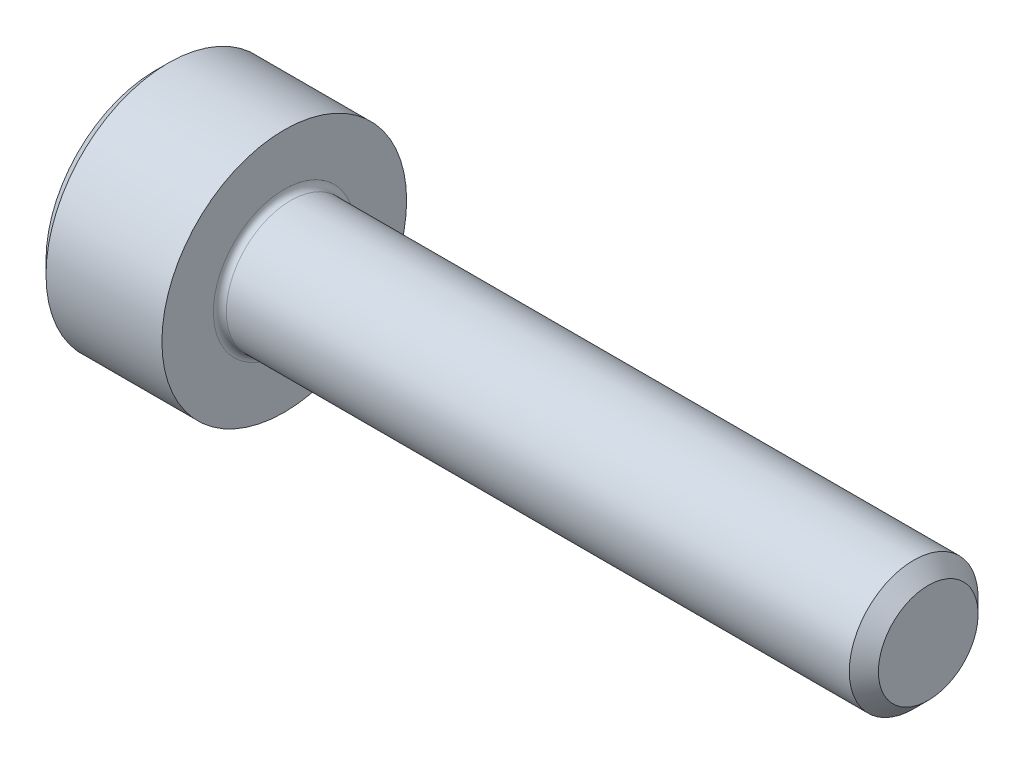
SolidWorks part; units mm, degrees
revolve "Base-Revolve" add sketch "BodySke"
sketch "BodySke" plane through (0, 0, 0) normal (0, 0, 1) x (1, 0, 0)
  line L0 (0, 0) -> (0, 1.7)
  line L1 (0.2, 1.9) -> (2, 1.9)
  line L2 (2, 1.9) -> (2, 1)
  line L3 (2, 1) -> (11.774, 1)
  line L4 (12, 0.774) -> (12, 0)
  line L5 (12, 0) -> (0, 0)
  line L6 (-31.75, 0) -> (127, 0) construction
  line L7 (0, 1.7) -> (0.2, 1.9)
  line L8 (12, 0.774) -> (11.774, 1)
  line L9 (0, -1.7) -> (0.2, -1.9) construction
  line L10 (12, -0.774) -> (11.774, -1) construction
  line L11 (2.4, 9.525) -> (2.4, 3.175) construction
  line L12 (2, 9.525) -> (2, 3.175) construction
  line L13 (-38, 9.525) -> (-38, 3.175) construction
  dimension "Diameter" = 2
  dimension "Head_ht" = 2
  dimension "Length" = 10
  dimension "Body_ch_ang" = 45
  dimension "Head_dia" = 3.8
  dimension "Head_ch_ang" = 45
  dimension "Minor_dia" = 1.548
  dimension "Advance" = 0.4
  dimension "Thread_nom" = 10
  dimension "Thread_length" = 50
  dimension "Head_ch_ht" = 0.2
cosmetic thread "ThreadCosmetic"
fillet "Fillet1" radius 0.1 1 edges at (2, 0, 1)
ref_plane "Plane1" through (0, 0, 0) normal (0, 0, 1) x (1, 0, 0)
ref_plane "Plane2" through (0, 0, 0) normal (0, 1, 0) x (1, 0, 0)
ref_plane "Plane3" through (0, 0, 0) normal (1, 0, 0) x (0, 0, -1)
sketch "Sketch2" plane through (0, 0, 0) normal (0, 0, 1) x (1, 0, 0)
  line L0 (0, 0.7725) -> (1, 0.7725)
  line L1 (1, 0.7725) -> (1.446, 0)
  line L2 (-31.75, 0) -> (127, 0) construction
  line L3 (1.446, 0) -> (0, 0)
  line L4 (0, 0) -> (0, 0.7725)
  line L5 (0, 1.7) -> (0, -1.7) construction
  line L6 (0, 0) -> (47.625, 0) construction
  line L7 (2, -1.9) -> (2, 1.9) construction
  dimension "D1" = 0.7725
  dimension "D2" = 60
revolve "Hex-PreBroach" cut sketch "Sketch2" angle 360 about L6
sketch "Sketch3" plane through (0, 0, 0) normal (-1, 0, 0) x (0, 0.5, 0.866)
  line L0 (0.446, 0.7725) -> (-0.446, 0.7725)
  line L1 (-0.446, 0.7725) -> (-0.892, 0)
  line L2 (0.446, 0.7725) -> (0.892, 0)
  line L3 (0.446, -0.7725) -> (0.892, 0)
  line L4 (0.446, -0.7725) -> (-0.446, -0.7725)
  line L5 (-0.446, -0.7725) -> (-0.892, 0)
  dimension "D1" = 0.7725
  dimension "D2" = 0.7725
  dimension "Hex_size" = 1.545
extrude "Hex" cut sketch "Sketch3" against normal blind 1
sketch "Sketch4" plane through (0, 0, 0) normal (-1, 0, 0) x (0, 0, 1)
  line L0 (0, 0) -> (0.9398, 0)
  line L1 (0, 0) -> (6.1484, 3.5498) construction
  line L2 (0, 0) -> (0.4699, 0.8139)
  line L3 (0.7832, 0.2175) -> (0.8962, 0.2828)
  line L4 (0.58, 0.5695) -> (0.693, 0.6348)
  arc A0 (0.7832, 0.2175) -> (0.58, 0.5695) centre (0, 0) ccw
  arc A1 (0.9398, 0) -> (0.8962, 0.2828) centre (0, 0) ccw
  arc A2 (0.4699, 0.8139) -> (0.693, 0.6348) centre (0, 0) cw
  dimension "D1" = 30
  dimension "D2" = 60
  dimension "Spline_p_dim" = 0.4064
  dimension "D3" = 0.2032
extrude "Spline" [suppressed] cut sketch "Sketch4" against normal blind 1
pattern_circular "CirPattern1" [suppressed] count 6 every 60
sketch "Sketch5" plane through (0, 0, 0) normal (0, 0, 1) x (1, 0, 0)
  line L0 (-31.75, 0) -> (127, 0) construction
  line L2 (0, 1.7) -> (0, -1.7) construction
  circle A0 centre (0.1, 0) radius 0.005
  dimension "Drilled_hole_dia" = 0.01
  dimension "Drilled_hole_loc" = 0.1
extrude "Hole" [suppressed] cut sketch "Sketch5" against normal through all and the other way through all
pattern_circular "Drilled-4" [suppressed] count 2 every 60
pattern_circular "Drilled-6" [suppressed] count 3 every 60
sketch "ThdSchSke" plane through (0, 0, 0) normal (0, 0, 1) x (1, 0, 0)
  line L0 (2.4, -0.774) -> (2.2418, -1)
  line L1 (2.4, -0.774) -> (2.5582, -1)
  line L2 (2.5582, -1) -> (2.5582, -1.25)
  line L3 (-3.175, 0) -> (5.1513, 0) construction
  line L5 (2.5582, -1.25) -> (2.2418, -1.25)
  line L6 (2.2418, -1.25) -> (2.2418, -1)
  line L7 (0, 1.7) -> (0, -1.7) construction
  dimension "Thread_minor" = 1.548
  dimension "Diameter" = 2
  dimension "Start" = 2.4
revolve "ThreadSchematic" [suppressed] cut sketch "ThdSchSke" angle 360 about L3
pattern_linear "ThdSchPat" [suppressed]
equation "\"D2@Sketch3\" = \"Hex_size@Sketch3\" / 2"
equation "\"D1@Sketch3\" = \"Hex_size@Sketch3\" / 2"
equation "\"D1@Sketch2\" = \"Hex_size@Sketch3\" / 2"
equation "\"D3@Sketch4\" = \"Spline_p_dim@Sketch4\" / 2"
equation "\"Thread_minor@ThreadCosmetic\"  =  \"Minor_dia@BodySke\""
equation "\"D2@CirPattern1\" = 360 / \"Num_teeth@CirPattern1\""
equation "\"Wall_thickness@Sketch2\" = \"Head_ht@BodySke\" - \"Key_eng@Hex\""
equation "\"Thread_length@ThreadCosmetic\" = ((sgn( (\"Length@BodySke\" - \"Advance@BodySke\" ) - \"Thread_nom@BodySke\" )-1)*( (\"Length@BodySke\" - \"Advance@BodySke\" ) - \"Thread_nom@BodySke\" ))/-2+ \"Thread_nom@BodySke\""
equation "\"Thread_minor@ThdSchSke\" = \"Minor_dia@BodySke\""
equation "\"Diameter@ThdSchSke\" = \"Diameter@BodySke\""
equation "\"Overcut@ThdSchSke\" = \"Diameter@BodySke\" * 1.25"
equation "\"Start@ThdSchSke\" = \"Head_ht@BodySke\" + \"Length@BodySke\" - \"Thread_length@ThreadCosmetic\"  '---Non-countersunk---"
equation "\"Num_threads@ThdSchPat\" = int( \"Thread_length@ThreadCosmetic\" / \"Advance@BodySke\" + 0.999 )  + 1"
equation "\"Advance@ThdSchPat\" = \"Thread_length@ThreadCosmetic\" /  (\"Num_threads@ThdSchPat\" - 1) 'relax it"
equation "\"Num_threads@ThdSchPat\" = \"Num_threads@ThdSchPat\" - sgn( \"Num_threads@ThdSchPat\" - 1) '---chamfered tips only---"
